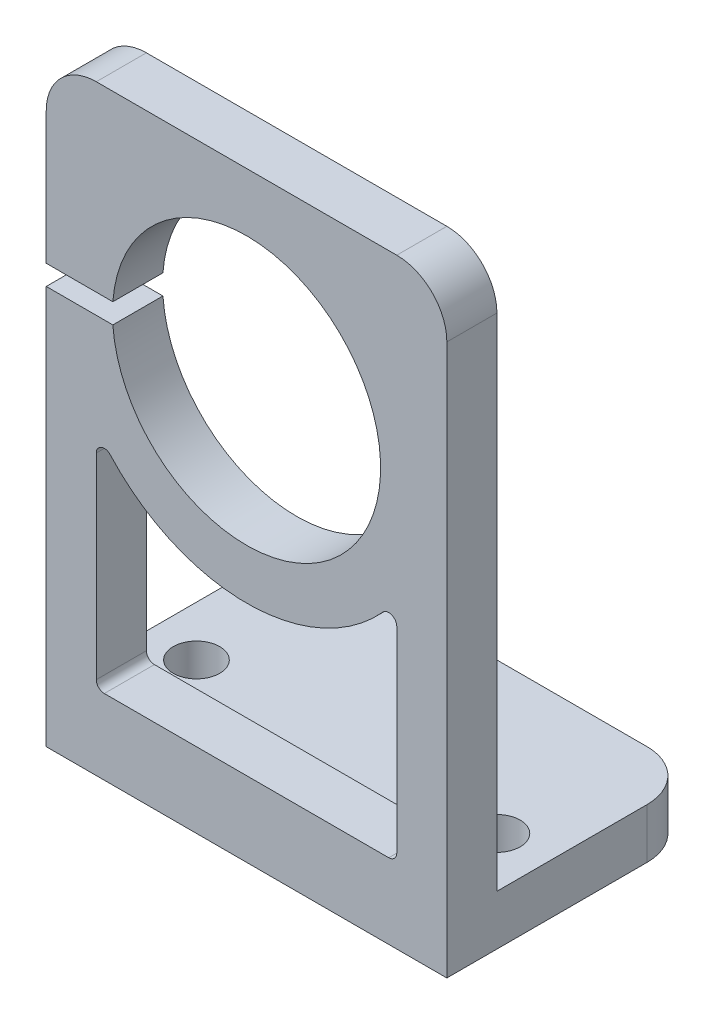
SolidWorks part; units mm, degrees
material "6061-T6 (SS)"
ref_plane "Front Plane" through (0, 0, 0) normal (0, 0, 1) x (1, 0, 0)
ref_plane "Top Plane" through (0, 0, 0) normal (0, 1, 0) x (1, 0, 0)
ref_plane "Right Plane" through (0, 0, 0) normal (1, 0, 0) x (0, 0, -1)
sketch "Sketch1" plane through (0, 0, 0) normal (1, 0, 0) x (0, 0, -1)
  line L0 (0, 38.1) -> (0, 0)
  line L1 (0, 0) -> (15.875, 0)
  line L2 (15.875, 0) -> (15.875, 3.175)
  line L3 (15.875, 3.175) -> (3.175, 3.175)
  line L4 (3.175, 3.175) -> (3.175, 38.1)
  line L5 (3.175, 38.1) -> (0, 38.1)
  dimension "D1" = 38.1
  dimension "D2" = 12.7
  dimension "D3" = 3.175
extrude "Boss-Extrude1" add sketch "Sketch1" along normal mid plane 25.4
sketch "Sketch2" plane through (0, 0, 0) normal (0, 0, 1) x (1, 0, 0)
  line L0 (12.7, 0) -> (-12.7, 0) construction
  circle A0 centre (0, 25.908) radius 8.5
  dimension "D2" = 17
  dimension "D1" = 25.908
extrude "Cut-Extrude1" cut sketch "Sketch2" against normal through all
fillet "Fillet1" radius 3.175 4 edges at (-12.7, 1.5875, -15.875) (12.7, 1.5875, -15.875) (-12.7, 38.1, -1.5875) (12.7, 38.1, -1.5875)
hole_wizard "#4 Clearance Hole1" positions "Sketch3" profile "Sketch4" hole size "#4" standard "ANSI Inch" end condition through all
sketch "Sketch3" plane through (0, 3.175, 0) normal (0, 1, 0) x (1, 0, 0)
  line L0 (-9.525, 6.35) -> (0, 0)
  line L1 (0, 0) -> (9.525, 6.35)
  line L3 (12.7, 3.175) -> (-12.7, 3.175) construction
  point P0 (-9.525, 6.35)
  point P2 (0, 12.7)
  point P4 (9.525, 6.35)
  dimension "D1" = 19.05
  dimension "D2" = 6.35
  dimension "D3" = 3.175
sketch "Sketch4" plane through (-9.525, 3.175, -6.35) normal (1, 0, 0) x (0, 0, 1)
  line L0 (0, 0) -> (0, 3.175)
  line L1 (0, 3.175) -> (1.4732, 3.175)
  line L2 (1.4732, 3.175) -> (1.4732, 0)
  line L5 (1.4732, 0) -> (0, 0)
  line L11 (0, -6.35) -> (0, 107.95) construction
  dimension "Thru Hole Dia." = 2.9464
  dimension "Thru Hole Depth" = 3.175
sketch "Sketch5" plane through (0, 0, 0) normal (0, 0, 1) x (1, 0, 0)
  line L1 (-24.8824, 26.543) -> (0, 26.543)
  line L2 (-24.8824, 26.543) -> (-24.8824, 25.273)
  line L3 (-24.8824, 25.273) -> (0, 25.273)
  line L4 (0, 26.543) -> (0, 25.273)
  line L5 (-24.8824, 26.543) -> (0, 25.273) construction
  line L6 (-24.8824, 25.273) -> (0, 26.543) construction
  point P0 (-12.4412, 25.908)
  point P5 (0, 25.908)
  dimension "D1" = 1.27
extrude "Cut-Extrude2" cut sketch "Sketch5" against normal through all
sketch "Sketch6" plane through (0, 0, 0) normal (0, 0, 1) x (1, 0, 0)
  line L0 (-9.525, 19.1567) -> (-9.525, 4.7625)
  line L1 (-9.525, 4.7625) -> (9.525, 4.7625)
  line L2 (9.525, 4.7625) -> (9.525, 19.1567)
  line L3 (12.7, 34.925) -> (12.7, 0) construction
  line L4 (12.7, 3.175) -> (-12.7, 3.175) construction
  line L5 (-12.7, 25.273) -> (-12.7, 0) construction
  arc A0 (-9.525, 19.1567) -> (9.525, 19.1567) centre (0, 25.908) ccw
  arc A1 (-8.4762, 25.273) -> (-8.4762, 26.543) centre (0, 25.908) ccw construction
  dimension "D1" = 3.175
  dimension "D2" = 3.175
  dimension "D3" = 1.5875
  dimension "D4" = 3.175
extrude "Cut-Extrude3" cut sketch "Sketch6" against normal through all
fillet "Fillet2" radius 0.508 4 edges at (9.525, 4.7625, -1.5875) (-9.525, 4.7625, -1.5875) (-9.525, 19.1567, -1.5875) (9.525, 19.1567, -1.5875)
